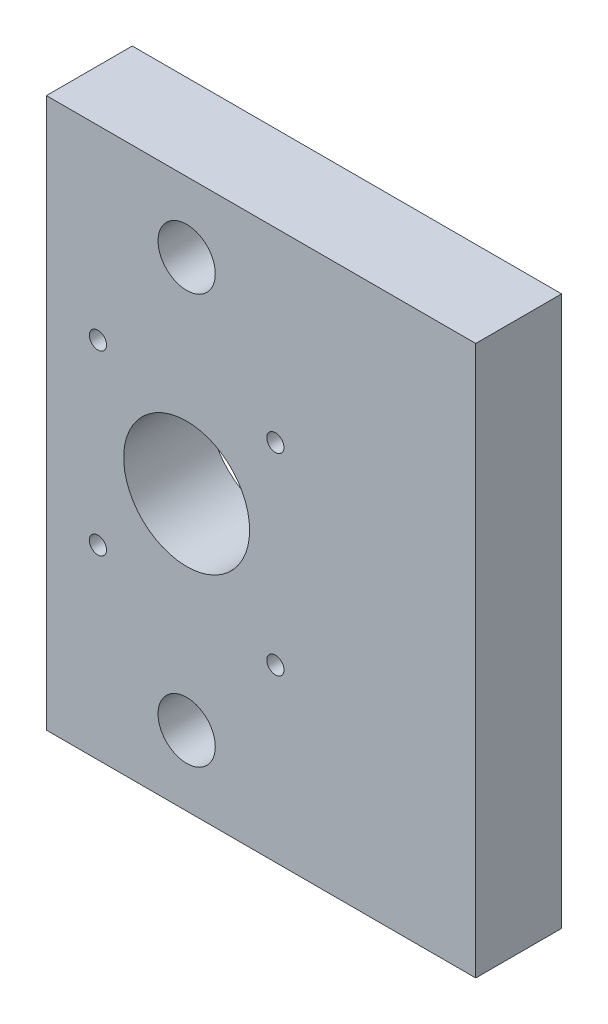
SolidWorks part; units mm, degrees
material "Balsa"
ref_plane "Front Plane" through (0, 0, 0) normal (0, 0, 1) x (1, 0, 0)
ref_plane "Top Plane" through (0, 0, 0) normal (0, 1, 0) x (1, 0, 0)
ref_plane "Right Plane" through (0, 0, 0) normal (1, 0, 0) x (0, 0, -1)
sketch "Sketch1" plane through (0, 0, 0) normal (0, 0, 1) x (1, 0, 0)
  line L0 (-60, 268.5094) -> (15, 268.5094) construction
  line L1 (15, 220.5094) -> (-60, 220.5094)
  line L2 (15, 220.5094) -> (15, 316.5094)
  line L3 (15, 316.5094) -> (-60, 316.5094)
  line L4 (-60, 220.5094) -> (-60, 316.5094)
  line L5 (-51, 253.0094) -> (-51, 284.0094) construction
  line L8 (0, 220.5094) -> (0, 316.5094) construction
  circle A0 centre (-51, 253.0094) radius 1.5
  circle A1 centre (-51, 284.0094) radius 1.5
  circle A2 centre (-20, 250.3707) radius 1.5
  circle A3 centre (-35.5, 268.5094) radius 11
  circle A4 centre (-20, 284.0094) radius 1.5
  circle A5 centre (-35.5, 232.7289) radius 5
  circle A6 centre (-35.5, 304.2898) radius 5
  point P38 (-51, 268.5094)
  dimension "D2" = 31
  dimension "D1" = 75
  dimension "D3" = 31
  dimension "D4" = 20
extrude "Boss-Extrude1" add sketch "Sketch1" along normal blind 15
